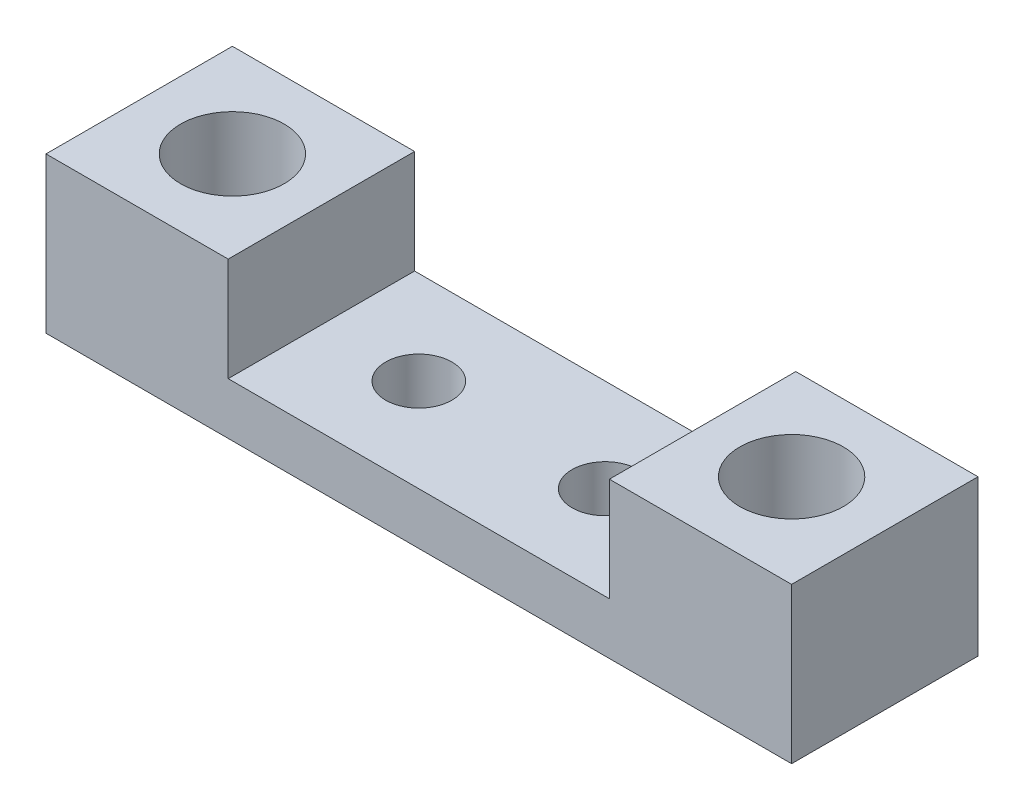
SolidWorks part; units mm, degrees
ref_plane "Front Plane" through (0, 0, 0) normal (0, 0, 1) x (1, 0, 0)
ref_plane "Top Plane" through (0, 0, 0) normal (0, 1, 0) x (1, 0, 0)
ref_plane "Right Plane" through (0, 0, 0) normal (1, 0, 0) x (0, 0, -1)
sketch "Sketch1" plane through (0, 0, 0) normal (0, 1, 0) x (1, 0, 0)
  line L1 (-26.8541, 4.5) -> (9.1459, 4.5)
  line L2 (-26.8541, 4.5) -> (-26.8541, -4.5)
  line L3 (-26.8541, -4.5) -> (9.1459, -4.5)
  line L4 (9.1459, 4.5) -> (9.1459, -4.5)
  circle A0 centre (-13.3541, 0) radius 1.6
  circle A1 centre (-4.3541, 0) radius 1.6
  circle A2 centre (4.6459, 0) radius 2.5
  circle A3 centre (-22.3541, 0) radius 2.5
  point P12 (0, 0)
  dimension "D1" = 5
  dimension "D2" = 5
  dimension "D3" = 3.2
  dimension "D4" = 3.2
  dimension "D5" = 9
  dimension "D6" = 9
  dimension "D7" = 9
  dimension "D8" = 4.5
  dimension "D10" = 4.5
  dimension "D9" = 4.5
  dimension "D11" = 4.5
extrude "Boss-Extrude1" add sketch "Sketch1" along normal blind 2.5
sketch "Sketch2" plane through (0, 2.5, 0) normal (0, 1, 0) x (1, 0, 0)
  line L0 (-26.8541, -4.5) -> (9.1459, -4.5) construction
  line L1 (-26.8541, 4.5) -> (-18.0574, 4.5)
  line L2 (-26.8541, 4.5) -> (-26.8541, -4.5)
  line L3 (-26.8541, -4.5) -> (-18.0574, -4.5)
  line L4 (-18.0574, 4.5) -> (-18.0574, -4.5)
  line L6 (9.1459, 4.5) -> (0.3491, 4.5)
  line L7 (9.1459, 4.5) -> (9.1459, -4.5)
  line L8 (9.1459, -4.5) -> (0.3491, -4.5)
  line L9 (0.3491, 4.5) -> (0.3491, -4.5)
  circle A0 centre (-22.3541, 0) radius 2.5
  circle A1 centre (4.6459, 0) radius 2.5
extrude "Boss-Extrude2" add sketch "Sketch2" along normal blind 5
